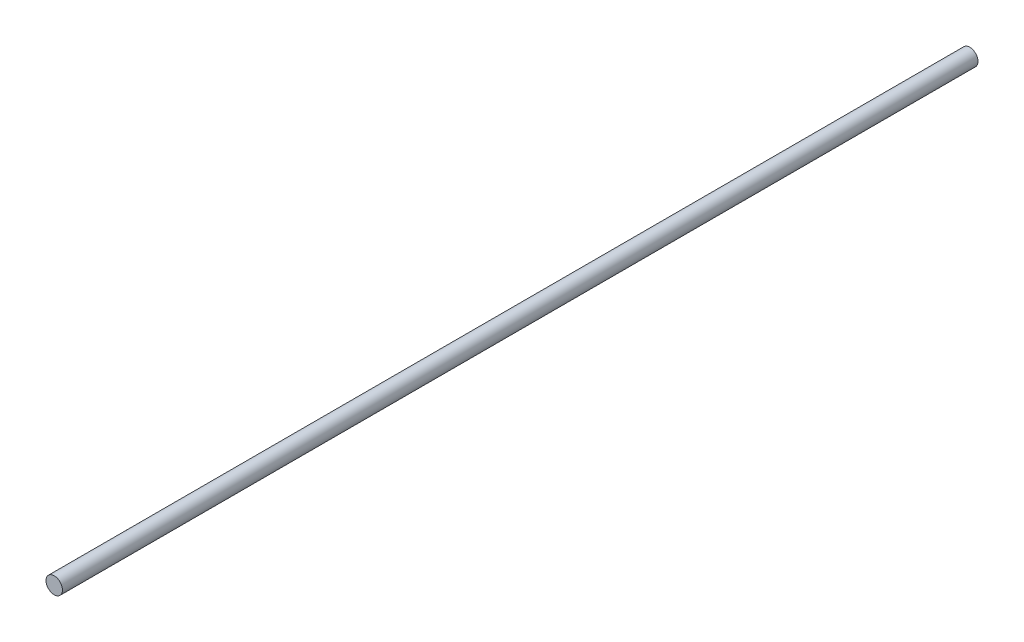
SolidWorks part; units mm, degrees
ref_plane "Front Plane" through (0, 0, 0) normal (0, 0, 1) x (1, 0, 0)
ref_plane "Top Plane" through (0, 0, 0) normal (0, 1, 0) x (1, 0, 0)
ref_plane "Right Plane" through (0, 0, 0) normal (1, 0, 0) x (0, 0, -1)
sketch "Sketch2" plane through (0, 0, 0) normal (0, 0, 1) x (1, 0, 0)
  circle A0 centre (0, 0) radius 22.5
  dimension "D1" = 45
extrude "Boss-Extrude1" add sketch "Sketch2" along normal blind 2500
